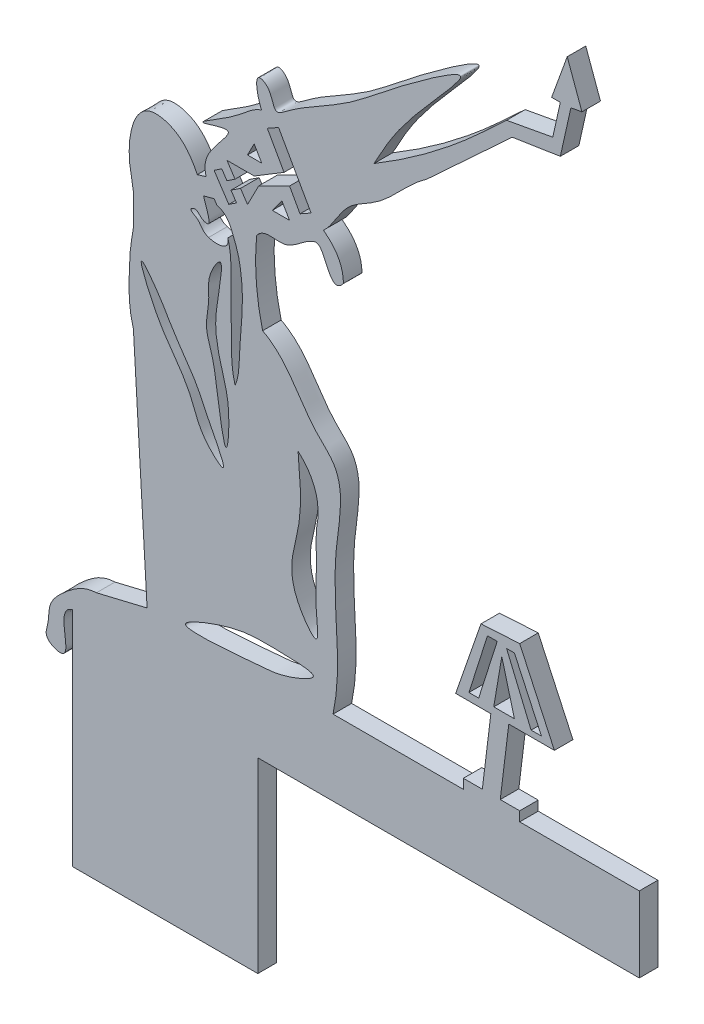
SolidWorks part; units mm, degrees
ref_plane "Alzado" through (0, 0, 0) normal (0, 0, 1) x (1, 0, 0)
ref_plane "Planta" through (0, 0, 0) normal (0, 1, 0) x (1, 0, 0)
ref_plane "Vista lateral" through (0, 0, 0) normal (1, 0, 0) x (0, 0, -1)
sketch "Croquis1" plane through (0, 0, 0) normal (0, 0, 1) x (1, 0, 0)
  line L0 (-1228.8467, -1013.4339) -> (-280.8467, -1013.4339) construction
  line L1 (-95.2999, 12.6894) -> (-94.3391, 12.9792)
  line L2 (-94.625, 11.0459) -> (-93.4893, 11.3487)
  line L3 (-93.4893, 11.3487) -> (-93.1783, 10.8902)
  line L5 (-108.7734, -43.6441) -> (-108.7734, -34.6603)
  line L6 (-106.173, -31.786) -> (-100.7096, -30.4751)
  line L7 (-100.7096, -30.4751) -> (-102.1878, -5.1555)
  line L8 (-108.7734, -43.6441) -> (-108.7734, -58.6441)
  line L10 (-47.6469, -38.4937) -> (-47.6469, -34.6603)
  line L11 (-47.6469, -34.6603) -> (-47.6469, -30.3623)
  line L12 (-47.6469, -30.3623) -> (-60.5395, -30.3623)
  line L13 (-60.5395, -30.3623) -> (-60.5395, -29.3273)
  line L14 (-60.5395, -29.3273) -> (-62.6358, -29.3273)
  line L15 (-62.6358, -29.3273) -> (-61.715, -21.8174)
  line L16 (-61.715, -21.8174) -> (-56.7977, -21.8174)
  line L17 (-56.7977, -21.8174) -> (-60.5395, -13.7148)
  line L18 (-60.5395, -13.7148) -> (-64.7128, -13.9584)
  line L19 (-64.7128, -13.9584) -> (-67.4416, -21.8174)
  line L20 (-67.4416, -21.8174) -> (-63.6471, -21.8174)
  line L21 (-63.6471, -21.8174) -> (-64.5679, -29.3273)
  line L22 (-64.5679, -29.3273) -> (-66.6135, -29.3273)
  line L23 (-66.6135, -29.3273) -> (-66.6135, -30.3623)
  line L24 (-66.6135, -30.3623) -> (-80.661, -30.3623)
  line L25 (-64.0127, -14.7184) -> (-66.0117, -21.0203)
  line L26 (-66.0117, -21.0203) -> (-64.9625, -21.0203)
  line L27 (-64.9625, -21.0203) -> (-62.9636, -14.7184)
  line L28 (-62.9636, -14.7184) -> (-64.0127, -14.7184)
  line L29 (-61.1056, -14.8779) -> (-58.1918, -21.1798)
  line L30 (-58.1918, -21.1798) -> (-59.3099, -21.1798)
  line L31 (-59.3099, -21.1798) -> (-61.9526, -14.8779)
  line L32 (-61.9526, -14.8779) -> (-61.1056, -14.8779)
  line L33 (-65.0122, -17.8693) -> (-65.9568, -17.5413)
  line L34 (-59.6487, -18.0289) -> (-58.7408, -17.6096)
  line L35 (-62.4696, -15.8901) -> (-63.3355, -21.0203)
  line L36 (-63.3355, -21.0203) -> (-61.1056, -21.0203)
  line L37 (-61.1056, -21.0203) -> (-62.4696, -15.8901)
  line L38 (-64.7128, 31.8828) -> (-61.9526, 34.4365)
  line L39 (-61.9526, 34.4365) -> (-57.6986, 35.2196)
  line L40 (-57.6986, 35.2196) -> (-56.9725, 35.3532)
  line L41 (-56.9725, 35.3532) -> (-56.1577, 39.0103)
  line L42 (-56.1577, 39.0103) -> (-57.095, 39.0103)
  line L43 (-57.095, 39.0103) -> (-55.4149, 43.6434)
  line L44 (-55.4149, 43.6434) -> (-53.829, 39.2906)
  line L45 (-53.829, 39.2906) -> (-55.0207, 39.0713)
  line L46 (-55.0207, 39.0713) -> (-56.1577, 33.968)
  line L47 (-56.1577, 33.968) -> (-61.3428, 33.1597)
  line L48 (-61.3428, 33.1597) -> (-70.5154, 24.673)
  line L49 (-85.9443, 17.5789) -> (-89.1672, 15.6285)
  line L50 (-89.1672, 15.6285) -> (-92.1053, 15.6285)
  line L51 (-92.1053, 15.6285) -> (-91.226, 14.3043)
  line L52 (-91.226, 14.3043) -> (-92.1053, 13.7204)
  line L53 (-92.1053, 13.7204) -> (-92.6572, 14.5515)
  line L54 (-92.6572, 14.5515) -> (-93.4893, 13.999)
  line L55 (-93.4893, 13.999) -> (-91.9031, 11.6102)
  line L56 (-91.9031, 11.6102) -> (-91.071, 12.1627)
  line L57 (-91.071, 12.1627) -> (-91.6656, 13.0583)
  line L58 (-91.6656, 13.0583) -> (-90.6363, 13.7418)
  line L59 (-90.6363, 13.7418) -> (-89.8851, 12.6105)
  line L60 (-89.8851, 12.6105) -> (-88.6643, 14.9664)
  line L61 (-88.6643, 14.9664) -> (-85.3541, 16.6037)
  line L62 (-89.1672, 18.6333) -> (-88.3502, 17.2331)
  line L63 (-88.3502, 17.2331) -> (-89.8851, 17.2331)
  line L64 (-89.8851, 17.2331) -> (-89.1672, 18.6333)
  line L65 (-86.1708, 14.7968) -> (-85.3541, 13.3972)
  line L66 (-85.3541, 13.3972) -> (-87.2101, 13.3972)
  line L67 (-87.2101, 13.3972) -> (-86.1708, 14.7968)
  line L68 (-85.9443, 17.5789) -> (-87.7511, 20.7919)
  line L69 (-87.7511, 20.7919) -> (-86.5346, 21.4759)
  line L70 (-86.5346, 21.4759) -> (-83.0281, 15.2403)
  line L71 (-83.0281, 15.2403) -> (-84.2265, 14.5664)
  line L72 (-84.2265, 14.5664) -> (-85.3541, 16.6037)
  line L76 (-108.7734, -58.6441) -> (-88.7734, -58.6441)
  line L77 (-88.7734, -58.6441) -> (-88.7734, -43.6441)
  line L78 (-47.6469, -38.4937) -> (-88.7734, -38.4937)
  line L79 (-88.7734, -38.4937) -> (-88.7734, -43.6441)
  spline S0 degree 3 poles (-108.7734, -34.6603) (-110.783, -35.188) (-107.8234, -40.446) (-111.9347, -38.7893) (-111.2496, -37.0922) (-111.437, -35.1735) (-109.2476, -33.0458) (-107.557, -31.8396) (-106.173, -31.786) knots 0 0 0 0 0.303956 0.416432 0.488649 0.600953 0.764816 1 1 1 1
  spline S1 degree 3 poles (-102.1878, -5.1555) (-102.7738, -3.191) (-102.6673, -0.5481) (-102.5184, 2.6133) (-102.1024, 4.2792) (-102.2324, 5.9103) (-102.0825, 7.8394) (-103.0584, 11.0776) (-102.1124, 16.8402) (-97.8462, 15.875) (-96.2498, 14.4306) (-95.5732, 13.2583) (-95.2999, 12.6894) knots 0 0 0 0 0.12089 0.161063 0.192252 0.224264 0.260224 0.307556 0.439617 0.492306 0.533661 0.571179 0.571179 0.571179 0.571179
  spline S2 degree 3 poles (-94.0656, 7.4553) (-93.5959, 7.2352) (-92.0654, 7.2018) (-91.9491, 8.1092) (-91.9991, 8.4408) knots 0 0 0 0 0.358046 0.527791 0.527791 0.527791 0.527791
  spline S3 degree 3 poles (-93.1783, 10.8902) (-92.1229, 10.6555) (-91.4982, 9.1847) (-90.7907, 7.2599) (-90.544, 5.6007) (-90.4043, 3.9374) (-90.4748, 1.5064) (-90.8044, -1.4579) (-90.7679, -3.909) (-91.226, -4.9381) knots 0 0 0 0 0.167695 0.269369 0.369433 0.465334 0.567826 0.803084 1 1 1 1
  spline S4 degree 3 poles (-91.226, -4.9381) (-91.6475, -3.5191) (-91.606, -1.4182) (-91.6428, 1.3385) (-91.6732, 4.3599) (-91.5462, 6.7462) (-91.9991, 8.4408) knots 0 0 0 0 0.324988 0.467576 0.616211 1 1 1 1
  spline S5 degree 3 poles (-94.2552, -9.436) (-91.3804, -14.6072) (-95.1279, -11.2554) (-95.659, -8.7175) (-97.673, -5.4874) (-99.5776, -3.2094) (-102.4254, 3.5103) (-99.1047, -0.9614) (-97.7728, -3.5509) (-95.383, -6.6182) (-94.2552, -9.436) (-91.3804, -14.6072) (-95.1279, -11.2554) knots -0.326741 -0.201873 -0.113902 0 0.06597 0.173694 0.257423 0.368748 0.501493 0.588429 0.673259 0.798127 0.886098 1 1.06597 1.173694 1.257423 only from (-92.58, -13.2995) to (-92.58, -13.2995)
  spline S6 degree 3 poles (-93.1712, -6.4085) (-92.0833, -14.054) (-91.7114, -7.1039) (-92.6214, -4.4452) (-93.3287, -1.5064) (-93.3913, 1.2159) (-92.0734, 7.4119) (-94.3168, 3.7324) (-93.8644, 1.5719) (-94.5984, -0.9056) (-93.5846, -3.526) (-93.1712, -6.4085) (-92.0833, -14.054) (-91.7114, -7.1039) knots -0.302053 -0.235055 -0.149128 0 0.125787 0.198193 0.280045 0.366872 0.494897 0.553279 0.621104 0.697947 0.764945 0.850872 1 1.125787 1.198193 1.280045 only from (-92.1702, -11.2158) to (-92.1702, -11.2158)
  spline S7 degree 3 poles (-84.4319, -7.7098) (-84.2164, -10.1145) (-83.7827, -14.9548) (-86.2335, -19.8495) (-81.9662, -25.5835) (-82.6753, -20.6861) (-82.3294, -17.915) (-82.5453, -15.1639) (-82.4483, -13.9584) knots 0 0 0 0 0.223816 0.450518 0.55019 0.627147 0.763698 0.878113 0.878113 0.878113 0.878113
  spline S8 degree 3 poles (-80.661, -30.3623) (-79.5043, -24.9563) (-81.552, -17.9147) (-79.0158, -7.9358) (-84.21, -3.6209) (-85.4577, 0.1789) (-88.2574, 1.634) knots 0 0 0 0 0.447834 0.672317 0.747682 1 1 1 1
  spline S9 degree 2 poles (-88.2574, 1.634) (-89.3165, 5.8903) (-88.8908, 10.2286) knots 0 0 0 1 1 1
  spline S10 degree 3 poles (-94.3391, 12.9792) (-94.528, 13.6054) (-94.5459, 15.6197) (-90.0045, 19.5013) (-96.7774, 16.9541) (-90.9037, 20.1073) (-89.6583, 21.6432) (-88.5479, 22.1291) (-88.3502, 22.2002) knots 0.128356 0.128356 0.128356 0.128356 0.235825 0.449269 0.587284 0.797011 0.963366 0.995107 0.995107 0.995107 0.995107
  spline S11 degree 3 poles (-88.3502, 22.2002) (-88.5183, 22.4048) (-89.0159, 23.9977) (-88.804, 25.3605) (-87.1705, 24.5589) (-87.1572, 22.2811) (-84.7319, 24.1636) (-82.6187, 25.4041) (-78.5656, 27.6963) (-74.7246, 31.0115) (-63.5881, 39.1482) (-72.5799, 29.3777) (-74.5352, 26.4738) (-76.2513, 23.2522) knots 0.009544 0.009544 0.009544 0.009544 0.045607 0.065002 0.086833 0.132572 0.1588 0.24215 0.321857 0.444077 0.65329 0.787621 1 1 1 1
  spline S12 degree 2 poles (-82.4483, -13.9584) (-81.6618, -10.151) (-84.4319, -7.7098) knots 0 0 0 1 1 1
  spline S13 degree 3 poles (-76.2513, 23.2522) (-72.0979, 25.7317) (-68.2517, 28.6085) (-64.7128, 31.8828) knots 0 0 0 0 1 1 1 1
  spline S14 degree 3 poles (-70.5154, 24.673) (-72.6326, 23.2454) (-74.7259, 20.0952) (-79.6032, 17.9626) (-80.5881, 15.2926) (-81.6951, 14.3043) knots 0 0 0 0 0.497652 0.706877 1 1 1 1
  spline S15 degree 2 poles (-81.6951, 14.3043) (-79.5439, 12.7057) (-79.5508, 10.3937) knots 0 0 0 1 1 1
  spline S16 degree 3 poles (-79.5508, 10.3937) (-81.1891, 8.2989) (-81.4235, 13.4856) (-82.7905, 12.6894) knots 0 0 0 0 1 1 1 1
  spline S17 degree 3 poles (-82.7905, 12.6894) (-83.8064, 12.3885) (-85.5853, 10.0159) (-88.071, 11.299) (-88.8908, 10.2286) knots 0 0 0 0 0.542449 1 1 1 1
  spline S18 degree 3 poles (-89.4524, -29.824) (-100.0053, -30.8873) (-90.9569, -27.2843) (-88.2041, -27.3527) (-81.0801, -27.5369) (-86.0868, -29.6552) (-89.4524, -29.824) (-100.0053, -30.8873) (-90.9569, -27.2843) knots -0.499194 -0.385687 -0.27403 0 0.15266 0.388237 0.500806 0.614313 0.72597 1 1.15266 1.388237 1.500806 only from (-96.5302, -29.822) to (-96.5302, -29.822)
  spline S19 degree 3 poles (-94.0656, 7.4553) (-94.8717, 7.6779) (-94.7662, 8.4598) (-96.2915, 9.0695) (-95.3068, 9.541) (-95.0054, 8.7862) (-93.929, 8.5085) (-94.1649, 9.8521) (-94.4183, 10.2949) (-94.625, 11.0459) knots 0 0 0 0 0.256336 0.360204 0.430018 0.55419 0.661729 0.733847 1 1 1 1
  dimension "D3" = 1
  dimension "D4" = 1
  dimension "D5" = 1
extrude "Saliente-Extruir1" add sketch "Croquis1" along normal blind 2
